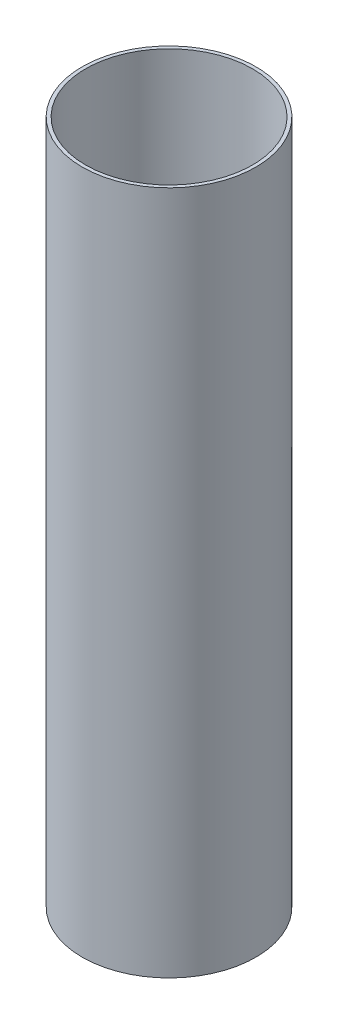
SolidWorks part; units mm, degrees
ref_plane "Front Plane" through (0, 0, 0) normal (0, 0, 1) x (1, 0, 0)
ref_plane "Top Plane" through (0, 0, 0) normal (0, 1, 0) x (1, 0, 0)
ref_plane "Right Plane" through (0, 0, 0) normal (1, 0, 0) x (0, 0, -1)
sketch "Sketch1" plane through (0, 0, 0) normal (0, 1, 0) x (1, 0, 0)
  circle A0 centre (0, 0) radius 39.6748
  circle A1 centre (0, 0) radius 38.1
  dimension "D1" = 79.3496
  dimension "D2" = 76.2
extrude "Boss-Extrude1" add sketch "Sketch1" along normal mid plane 312.42
equation "\"iDiameter\"= 3in"
equation "\"oDiameter\" = 3.124in"
equation "\"length\"= 12.3in"
equation "\"D1@Sketch1\"=\"oDiameter\""
equation "\"D2@Sketch1\"=\"iDiameter\""
equation "\"D1@Boss-Extrude1\"=\"length\""
